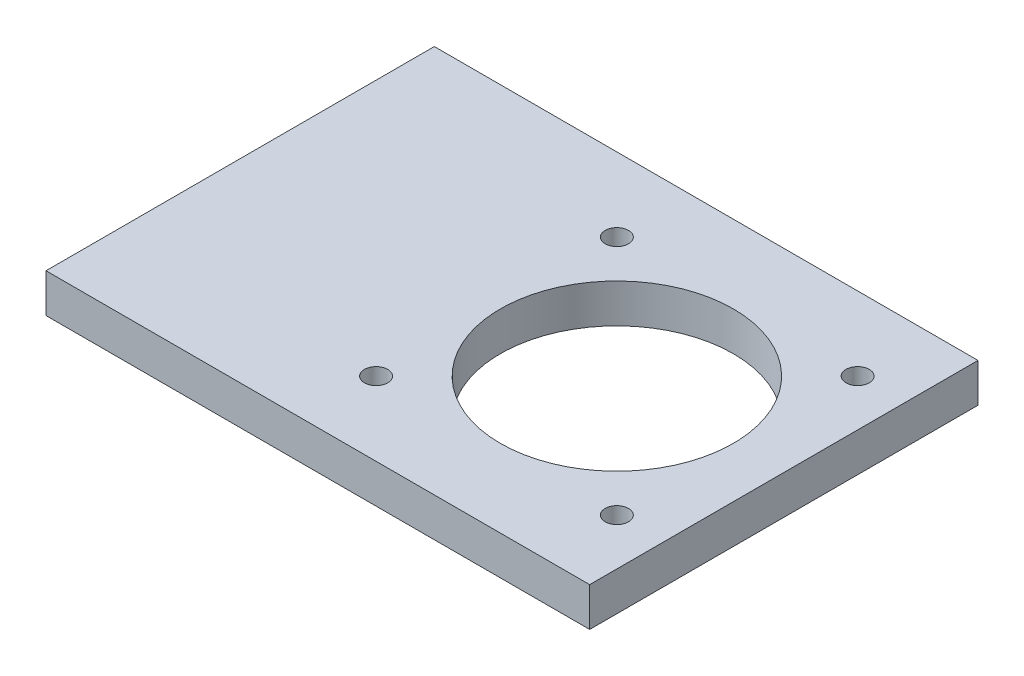
SolidWorks part; units mm, degrees
ref_plane "Front Plane" through (0, 0, 0) normal (0, 0, 1) x (1, 0, 0)
ref_plane "Top Plane" through (0, 0, 0) normal (0, 1, 0) x (1, 0, 0)
ref_plane "Right Plane" through (0, 0, 0) normal (1, 0, 0) x (0, 0, -1)
sketch "Sketch1" plane through (0, 0, 0) normal (0, 1, 0) x (1, 0, 0)
  line L1 (35, -25) -> (-35, -25)
  line L2 (35, -25) -> (35, 25)
  line L3 (35, 25) -> (-35, 25)
  line L4 (-35, -25) -> (-35, 25)
  line L5 (35, -25) -> (-35, 25) construction
  line L6 (35, 25) -> (-35, -25) construction
  point P0 (0, 0)
extrude "Boss-Extrude1" add sketch "Sketch1" along normal blind 5
sketch "Sketch2" plane through (0, 5, 0) normal (0, 1, 0) x (1, 0, 0)
  line L0 (35, -25) -> (35, 25) construction
  circle A0 centre (29, 15.5) radius 1.5
  circle A1 centre (-2, 15.5) radius 1.5
  dimension "D1" = 15.5
  dimension "D2" = 6
  dimension "D3" = 31
extrude "Cut-Extrude1" cut sketch "Sketch2" against normal blind 5
mirror "Mirror1" about plane through (0, 0, 0) normal (0, 0, 1) of "Cut-Extrude1"
sketch "Sketch3" plane through (0, 5, 0) normal (0, 1, 0) x (1, 0, 0)
  circle A0 centre (13.5, 0) radius 15
  circle A1 centre (-2, 15.5) radius 1.5 construction
  dimension "D1" = 15.5
extrude "Cut-Extrude2" cut sketch "Sketch3" against normal blind 5
